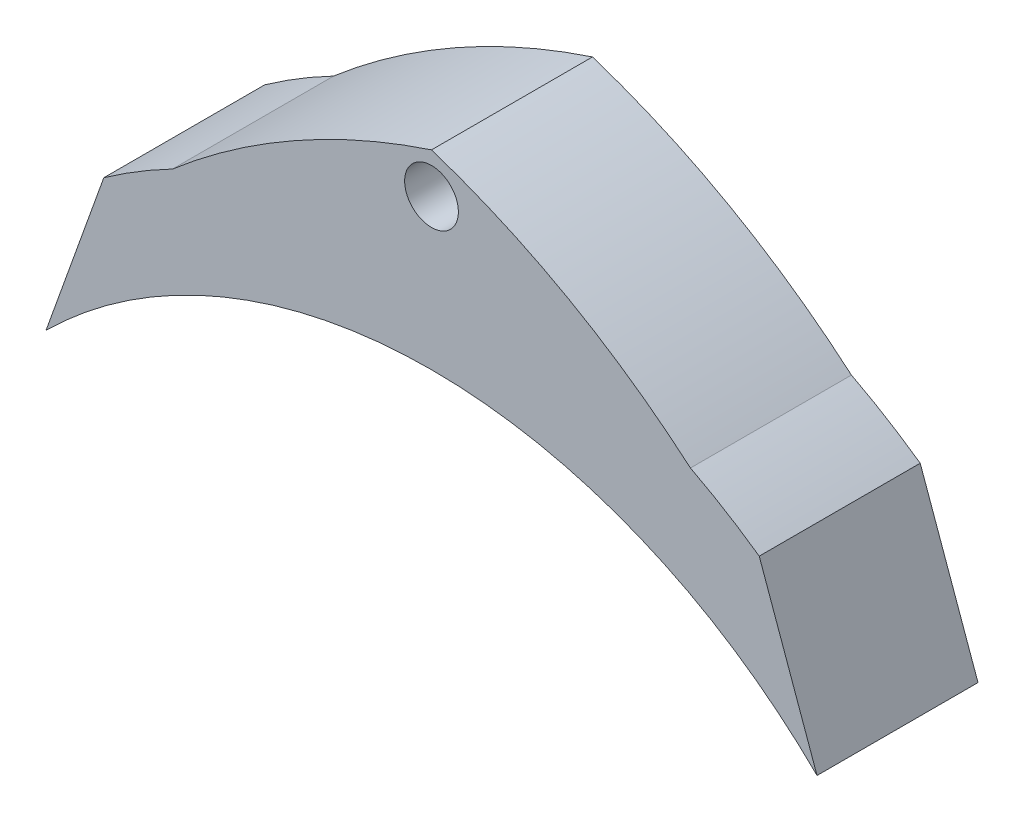
SolidWorks part; units mm, degrees
ref_plane "Front Plane" through (0, 0, 0) normal (0, 0, 1) x (1, 0, 0)
ref_plane "Top Plane" through (0, 0, 0) normal (0, 1, 0) x (1, 0, 0)
ref_plane "Right Plane" through (0, 0, 0) normal (1, 0, 0) x (0, 0, -1)
sketch "Sketch1" plane through (0, 0, 0) normal (0, 0, 1) x (1, 0, 0)
  line L0 (-71.843, 72.6566) -> (-61.0726, 102.6782)
  line L1 (0, 102.2299) -> (0, 122.6698)
  line L2 (0, 122.6698) -> (0, 125.1812)
  line L3 (0, 135.1986) -> (0, 137.71)
  arc A2 (-71.843, 72.6566) -> (0, 102.2299) centre (0, 0.1782) cw
  arc A3 (-61.0726, 102.6782) -> (0, 122.6698) centre (1.7422, 14.0663) cw
  arc A4 (0, 135.1986) -> (0, 125.1812) centre (0, 130.1899) ccw
  arc A5 (0, 137.71) -> (-48.2584, 110.4909) centre (44.3655, 2.6621) ccw
  arc A6 (-48.2584, 110.4909) -> (0, 122.6698) centre (1.7422, 14.0663) cw
  point P14 (0, 0)
  point P15 (0, 0)
  point P16 (0, 0)
extrude "Boss-Extrude1" add sketch "Sketch1" along normal blind 30 contours L3 A5 A3 L2 A4
ref_plane "Plane1" through (0, 0, 15) normal (0, 0, 1) x (1, 0, 0)
sketch "Sketch2" plane through (0, 0, 15) normal (0, 0, 1) x (1, 0, 0)
  line L0 (0, 104.319) -> (-16.4187, 104.319) construction
  line L1 (0, 102.2299) -> (0, 122.6698) construction
  line L2 (-16.4187, 115.4017) -> (-16.4187, 103.1682) construction
  line L4 (-20.5787, 100.069) -> (-12.2587, 100.069)
  line L5 (-20.5787, 100.069) -> (-20.5787, 108.569)
  line L6 (-20.5787, 108.569) -> (-12.2587, 108.569)
  line L7 (-12.2587, 100.069) -> (-12.2587, 108.569)
  line L8 (-20.5787, 100.069) -> (-12.2587, 108.569) construction
  line L9 (-20.5787, 108.569) -> (-12.2587, 100.069) construction
  line L12 (-29.0833, 97.998) -> (-9.7867, 97.998) construction
  line L15 (-29.0833, 97.998) -> (-20.7633, 97.998)
  line L24 (-29.0833, 97.998) -> (-29.0833, 108.398)
  line L25 (-29.0833, 108.398) -> (-20.7633, 108.398)
  line L26 (-20.7633, 97.998) -> (-20.7633, 108.398)
  line L27 (0, 102.1301) -> (-4.159, 102.1301)
  line L28 (0, 102.1301) -> (0, 110.4148)
  line L29 (0, 110.4148) -> (-4.159, 110.4148)
  line L30 (-4.159, 102.1301) -> (-4.159, 110.4148)
  arc A0 (0, 102.2299) -> (-71.843, 72.6566) centre (0, 0.1782) ccw construction
  dimension "D1" = 8.32
  dimension "D2" = 8.5
  dimension "D3" = 10.4
  dimension "D4" = 8.32
extrude "Cut-Extrude5" cut sketch "Sketch2" against normal blind 8.32 and the other way blind 8.32
sketch "Sketch4" plane through (0, 0, 0) normal (1, 0, 0) x (0, 0, -1)
  line L0 (0, 122.6698) -> (-5, 122.6698) construction
  line L1 (-30, 122.6698) -> (0, 122.6698) construction
  line L2 (-5, 122.6698) -> (-5, 142.6698) construction
mirror "Mirror3" about plane through (0, 0, 30) normal (-1, 0, 0) of bodies 107
